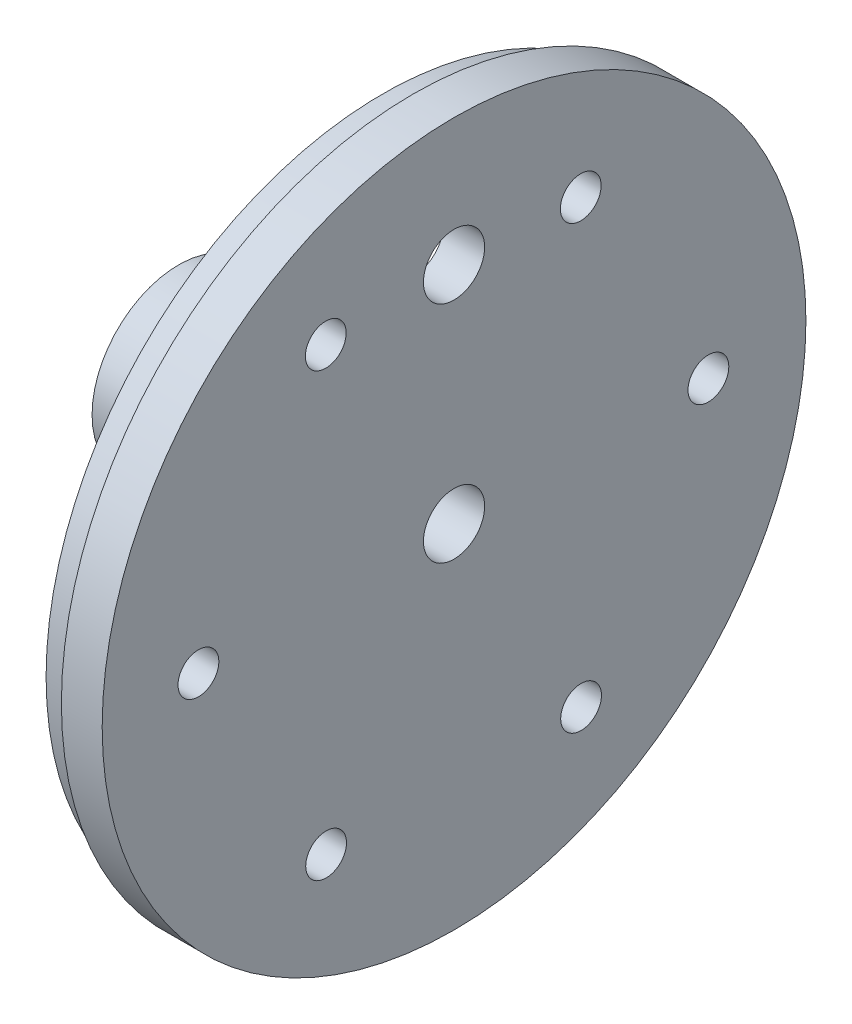
SolidWorks part; units mm, degrees
ref_plane "Front Plane" through (0, 0, 0) normal (0, 0, 1) x (1, 0, 0)
ref_plane "Top Plane" through (0, 0, 0) normal (0, 1, 0) x (1, 0, 0)
ref_plane "Right Plane" through (0, 0, 0) normal (1, 0, 0) x (0, 0, -1)
sketch "Sketch1" plane through (0, 0, 0) normal (1, 0, 0) x (0, 0, -1)
  circle A0 centre (0, 0) radius 34.5
extrude "Boss-Extrude1" add sketch "Sketch1" along normal mid plane 4
sketch "Sketch2" plane through (-2, 0, 0) normal (-1, 0, 0) x (0, 0, 1)
  circle A0 centre (0, 0) radius 8.49
  dimension "D1" = 16.98
extrude "Boss-Extrude2" add sketch "Sketch2" along normal blind 23
sketch "Sketch3" plane through (2, 0, 0) normal (1, 0, 0) x (0, 0, -1)
  circle A0 centre (0, 0) radius 10
sketch "Sketch4" plane through (-25, 0, 0) normal (-1, 0, 0) x (0, 0, 1)
  circle A0 centre (0, 0) radius 3
extrude "Cut-Extrude1" cut sketch "Sketch4" against normal blind 30
ref_plane "Plane1" through (0, 8.5, 0) normal (0, 1, 0) x (1, 0, 0)
sketch "Sketch5" plane through (0, 8.5, 0) normal (0, 1, 0) x (1, 0, 0)
  line L0 (-25, 8.49) -> (-25, -8.49) construction
  circle A0 centre (-19.5, 0) radius 1.5
  dimension "D1" = 5.5
extrude "Cut-Extrude2" cut sketch "Sketch5" against normal up to next
sketch "Sketch6" plane through (0, 0, 0) normal (0, 0, 1) x (1, 0, 0)
  line L0 (-25, 8.49) -> (-25, -8.49) construction
  circle A0 centre (-19.5, 0) radius 1.5
  dimension "D1" = 5.5
extrude "Cut-Extrude3" cut sketch "Sketch6" against normal up to next
sketch "Sketch19" plane through (-2, 0, 0) normal (-1, 0, 0) x (0, 0, 1)
  circle A0 centre (0, 0) radius 33
  circle A1 centre (0, 0) radius 30
  dimension "D2" = 66
  dimension "D1" = 3
extrude "Boss-Extrude5" add sketch "Sketch19" along normal blind 3
sketch "Sketch20" plane through (-2, 0, 0) normal (-1, 0, 0) x (0, 0, 1)
  circle A0 centre (-12.4224, 21.5162) radius 2
  circle A3 centre (12.5776, 21.4971) radius 2
  circle A4 centre (25.0611, -0.1631) radius 2
  circle A5 centre (12.5445, -21.8041) radius 2
  circle A6 centre (-12.4554, -21.785) radius 2
  circle A7 centre (-24.9389, -0.1249) radius 2
  point P22 (0.0611, -0.144)
  dimension "D2" = 6
sketch "Sketch21" plane through (-2, 0, 0) normal (-1, 0, 0) x (0, 0, 1)
  circle A0 centre (0, 22) radius 3
  dimension "D1" = 22
extrude "Cut-Extrude6" cut sketch "Sketch21" against normal blind 10
extrude "Cut-Extrude7" cut sketch "Sketch20" against normal blind 10
equation "\"÷6.00mm\"=6"
